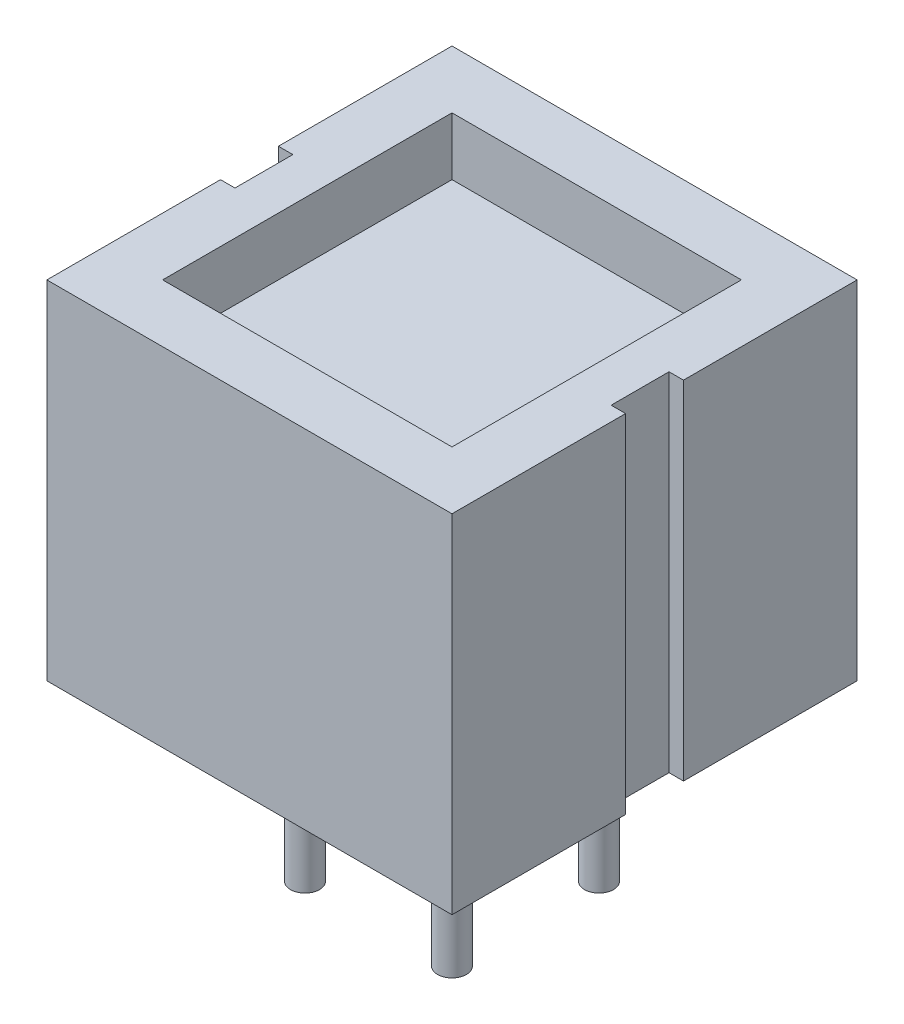
SolidWorks part; units mm, degrees
ref_plane "Alzado" through (0, 0, 0) normal (0, 0, 1) x (1, 0, 0)
ref_plane "Planta" through (0, 0, 0) normal (0, 1, 0) x (1, 0, 0)
ref_plane "Vista lateral" through (0, 0, 0) normal (1, 0, 0) x (0, 0, -1)
sketch "Croquis1" plane through (0, 0, 0) normal (0, 1, 0) x (1, 0, 0)
  line L1 (-3.5, -3.5) -> (3.5, -3.5)
  line L2 (-3.5, -3.5) -> (-3.5, 3.5)
  line L3 (-3.5, 3.5) -> (3.5, 3.5)
  line L4 (3.5, -3.5) -> (3.5, 3.5)
  line L5 (-3.5, -3.5) -> (3.5, 3.5) construction
  line L6 (-3.5, 3.5) -> (3.5, -3.5) construction
  point P0 (0, 0)
extrude "Saliente-Extruir1" add sketch "Croquis1" along normal blind 6
sketch "Croquis2" plane through (0, 0, 0) normal (0, -1, 0) x (1, 0, 0)
  line L5 (-1.27, -1.27) -> (1.27, 1.27) construction
  line L6 (-1.27, 1.27) -> (1.27, -1.27) construction
  circle A0 centre (-1.27, 1.27) radius 0.25
  circle A1 centre (1.27, 1.27) radius 0.25
  circle A2 centre (1.27, -1.27) radius 0.25
  circle A3 centre (-1.27, -1.27) radius 0.25
  point P0 (0, 0)
extrude "Saliente-Extruir2" add sketch "Croquis2" along normal blind 3
sketch "Croquis3" plane through (0, 6, 0) normal (0, 1, 0) x (1, 0, 0)
  line L1 (-2.5, -2.5) -> (2.5, -2.5)
  line L2 (-2.5, -2.5) -> (-2.5, 2.5)
  line L3 (-2.5, 2.5) -> (2.5, 2.5)
  line L4 (2.5, -2.5) -> (2.5, 2.5)
  line L5 (-2.5, -2.5) -> (2.5, 2.5) construction
  line L6 (-2.5, 2.5) -> (2.5, -2.5) construction
  point P0 (0, 0)
extrude "Cortar-Extruir1" cut sketch "Croquis3" against normal blind 1
sketch "Croquis4" plane through (0, 6, 0) normal (0, 1, 0) x (1, 0, 0)
  line L0 (0, -3.5) -> (0, 3.5) construction
  line L1 (-3.5, -3.5) -> (3.5, -3.5) construction
  line L2 (3.5, 3.5) -> (-3.5, 3.5) construction
  line L3 (3.5, -3.5) -> (3.5, 3.5) construction
  line L4 (3.75, -0.5) -> (3.25, -0.5)
  line L5 (3.75, -0.5) -> (3.75, 0.5)
  line L6 (3.75, 0.5) -> (3.25, 0.5)
  line L7 (3.25, -0.5) -> (3.25, 0.5)
  line L8 (3.75, -0.5) -> (3.25, 0.5) construction
  line L9 (3.75, 0.5) -> (3.25, -0.5) construction
  line L10 (-3.75, 0.5) -> (-3.25, 0.5)
  line L11 (-3.25, -0.5) -> (-3.25, 0.5)
  line L12 (-3.75, -0.5) -> (-3.25, -0.5)
  line L13 (-3.75, -0.5) -> (-3.75, 0.5)
  line L14 (-3.75, 0.5) -> (-3.25, -0.5) construction
  line L15 (-3.75, -0.5) -> (-3.25, 0.5) construction
  point P6 (3.5, 0)
  point P17 (-3.5, 0)
extrude "Cortar-Extruir2" cut sketch "Croquis4" against normal through all
